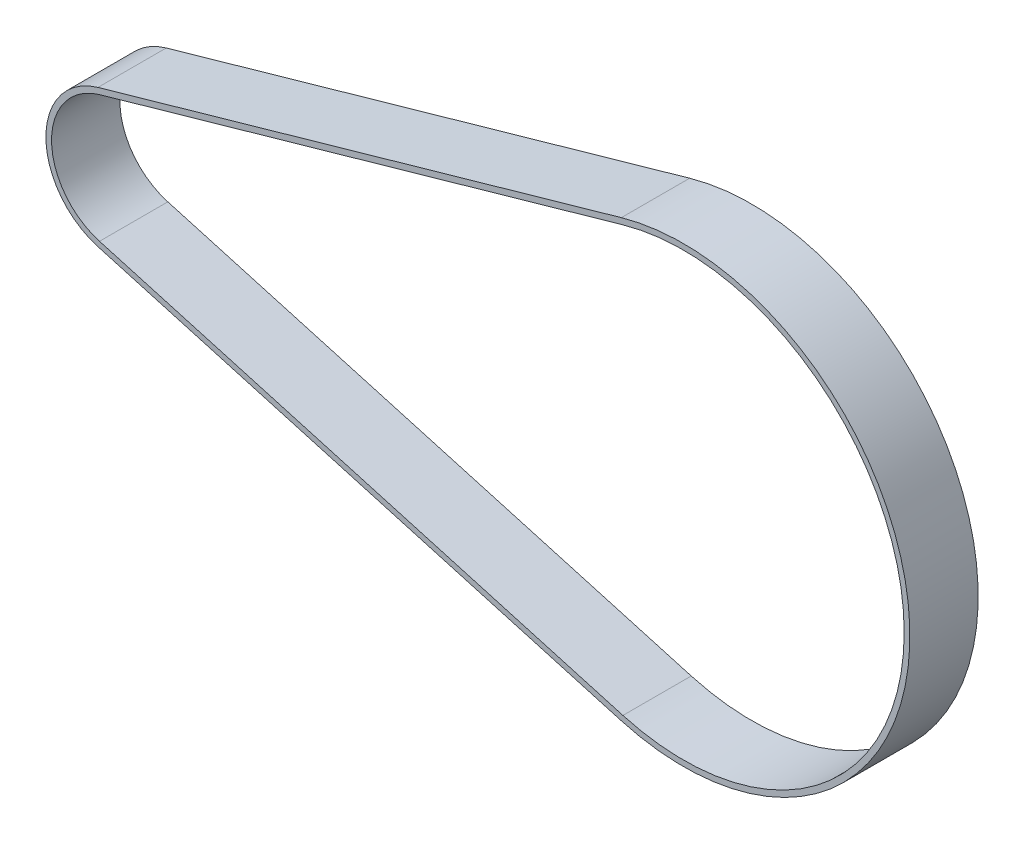
SolidWorks part; units mm, degrees
ref_plane "Front Plane" through (0, 0, 0) normal (0, 0, 1) x (1, 0, 0)
ref_plane "Top Plane" through (0, 0, 0) normal (0, 1, 0) x (1, 0, 0)
ref_plane "Right Plane" through (0, 0, 0) normal (1, 0, 0) x (0, 0, -1)
sketch "Sketch1" plane through (0, 0, 0) normal (0, 0, 1) x (1, 0, 0)
  line L0 (-1.5871, 5.5786) -> (44.3913, 18.6595)
  line L1 (0, 0) -> (-1.5871, 5.5786) construction
  line L2 (49.7, 0) -> (44.3913, 18.6595) construction
  line L3 (0, 0) -> (49.7, 0) construction
  line L4 (49.7, 0) -> (44.3913, -18.6595) construction
  line L5 (-1.5871, -5.5786) -> (44.3913, -18.6595)
  line L6 (0, 0) -> (-1.5871, -5.5786) construction
  line L7 (-1.7239, 6.0595) -> (44.2545, 19.1404)
  line L8 (-1.7239, -6.0595) -> (44.2545, -19.1404)
  arc A0 (-1.5871, 5.5786) -> (-1.5871, -5.5786) centre (0, 0) ccw
  arc A1 (44.3913, -18.6595) -> (44.3913, 18.6595) centre (49.7, 0) ccw
  arc A2 (44.2545, -19.1404) -> (44.2545, 19.1404) centre (49.7, 0) ccw
  arc A3 (-1.7239, 6.0595) -> (-1.7239, -6.0595) centre (0, 0) ccw
  dimension "D1" = 11.6
  dimension "D2" = 38.8
  dimension "D3" = 49.7
  dimension "D4" = 47.803
  dimension "D5" = 148.238
  dimension "D6" = 211.762
  dimension "D7" = 0.5
extrude "Boss-Extrude1" add sketch "Sketch1" along normal blind 6
